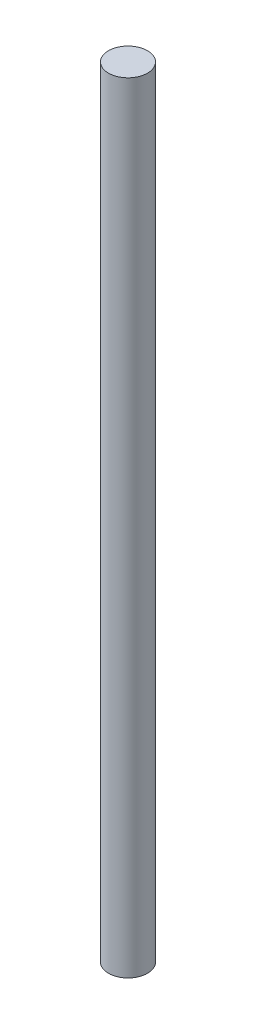
SolidWorks part; units mm, degrees
ref_plane "Front Plane" through (0, 0, 0) normal (0, 0, 1) x (1, 0, 0)
ref_plane "Top Plane" through (0, 0, 0) normal (0, 1, 0) x (1, 0, 0)
ref_plane "Right Plane" through (0, 0, 0) normal (1, 0, 0) x (0, 0, -1)
sketch "Sketch1" plane through (0, 0, 0) normal (0, 1, 0) x (1, 0, 0)
  circle A0 centre (0, 0) radius 6.35
  dimension "D1" = 12.7
extrude "Boss-Extrude1" add sketch "Sketch1" along normal blind 254
